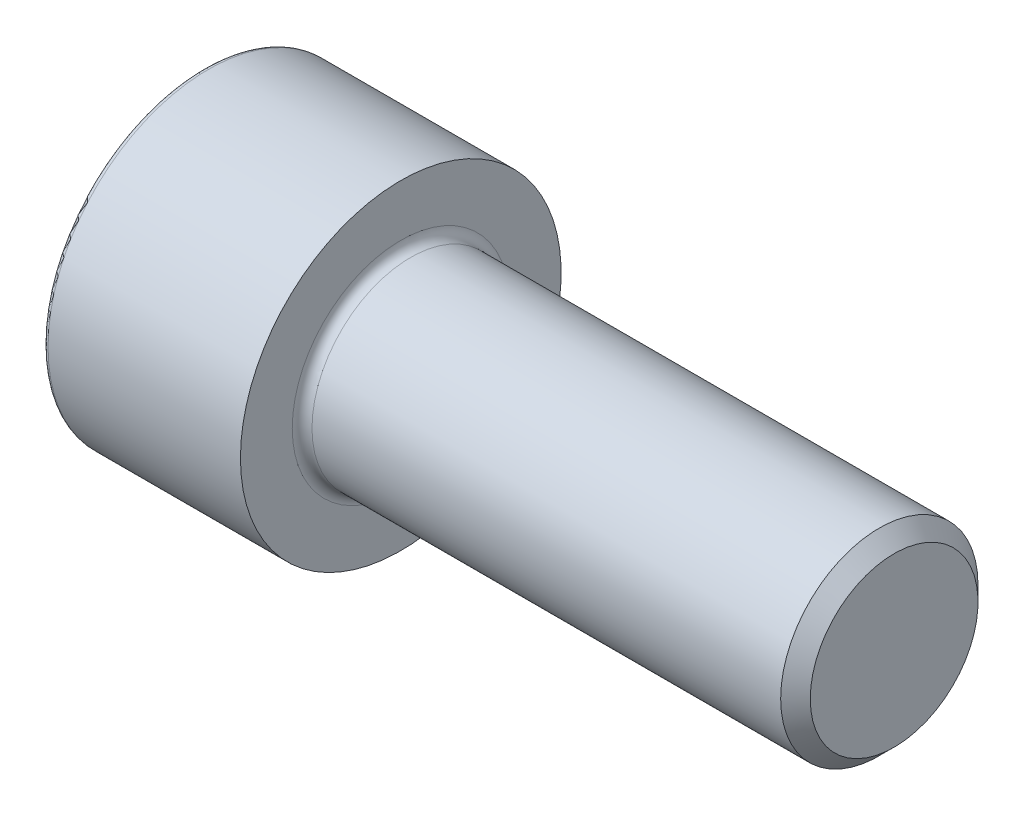
SolidWorks part; units mm, degrees
ref_plane "Front Plane" through (0, 0, 0) normal (0, 0, 1) x (1, 0, 0)
ref_plane "Top Plane" through (0, 0, 0) normal (0, 1, 0) x (1, 0, 0)
ref_plane "Right Plane" through (0, 0, 0) normal (1, 0, 0) x (0, 0, -1)
sketch "草图1" plane through (0, 0, 0) normal (0, 0, 1) x (1, 0, 0)
  line L0 (0, 0) -> (85.0281, 0) construction
  line L1 (0, 0) -> (0, 6.5)
  line L2 (0, 6.5) -> (8, 6.5)
  line L3 (8, 6.5) -> (8, 4)
  line L4 (8, 4) -> (28, 4)
  line L5 (28, 4) -> (28, 0)
  line L6 (28, 0) -> (0, 0)
  dimension "D1" = 8
  dimension "D2" = 13
  dimension "D3" = 8
  dimension "D4" = 20
revolve "旋转1" add sketch "草图1" angle 360 about L0
hole_wizard "大小mm 暗销孔1" positions "草图3" profile "草图2" hole size "Ø6.0" standard "GB"
sketch "草图3" plane through (0, 0, 0) normal (-1, 0, 0) x (0, 0, 1)
  point P0 (0, 0)
sketch "草图2" plane through (0, 0, 0) normal (0, 1, 0) x (0, 0, 1)
  line L0 (0, 0) -> (0, 5.8026)
  line L1 (0, 5.8026) -> (3, 4)
  line L2 (3, 4) -> (3, 0)
  line L5 (3, 0) -> (0, 0)
  line L10 (0, 5.8026) -> (-3, 4) construction
  line L11 (0, -6.35) -> (0, 107.95) construction
  dimension "孔直径" = 6
  dimension "孔深度" = 4
  dimension "导头角度" = 118
sketch "草图4" plane through (0, 0, 0) normal (-1, 0, 0) x (0, 0, 1)
  line L0 (0, 3.4641) -> (0, -3.4641) construction
  line L1 (3, 1.7321) -> (0, 3.4641)
  line L2 (0, 3.4641) -> (-3, 1.7321)
  line L3 (-3, 1.7321) -> (-3, -1.7321)
  line L4 (-3, -1.7321) -> (0, -3.4641)
  line L5 (0, -3.4641) -> (3, -1.7321)
  line L6 (3, -1.7321) -> (3, 1.7321)
  circle A0 centre (0, 0) radius 3 construction
  dimension "D1" = 6
extrude "切除-拉伸1" cut sketch "草图4" against normal blind 4
fillet "圆角1" radius 0.2 1 edges at (0, 0, 6.5)
chamfer "倒角1" distance 0.6 angle 45 1 edges at (28, 0, 4)
fillet "圆角2" radius 0.4 1 edges at (8, 0, 4)
